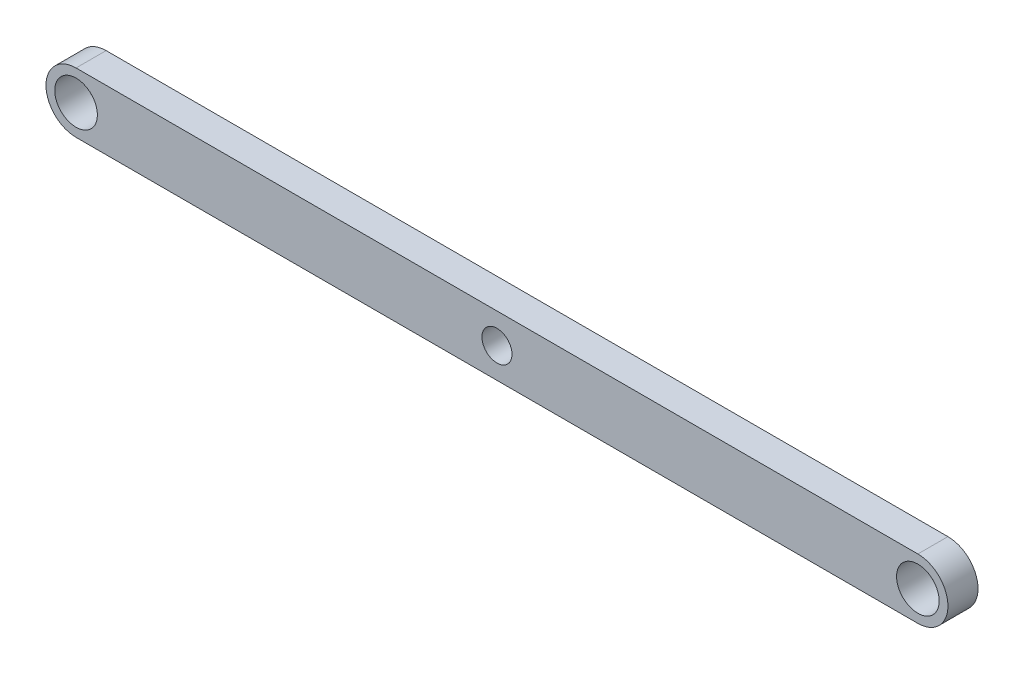
SolidWorks part; units mm, degrees
ref_plane "Front Plane" through (0, 0, 0) normal (0, 0, 1) x (1, 0, 0)
ref_plane "Top Plane" through (0, 0, 0) normal (0, 1, 0) x (1, 0, 0)
ref_plane "Right Plane" through (0, 0, 0) normal (1, 0, 0) x (0, 0, -1)
sketch "Sketch1" plane through (0, 0, 0) normal (0, 0, 1) x (1, 0, 0)
  line L0 (-88.9, 0) -> (88.9, 0) construction
  line L1 (-88.9, 6.35) -> (88.9, 6.35)
  line L2 (-88.9, -6.35) -> (88.9, -6.35)
  arc A0 (-88.9, 6.35) -> (-88.9, -6.35) centre (-88.9, 0) ccw
  arc A1 (88.9, -6.35) -> (88.9, 6.35) centre (88.9, 0) ccw
  circle A2 centre (-88.9, 0) radius 4.5
  circle A3 centre (88.9, 0) radius 4.5
  circle A4 centre (0, 0) radius 3.175
  point P2 (0, 0)
  dimension "D3" = 9
  dimension "D4" = 6.35
  dimension "D1" = 177.8
  dimension "D2" = 12.7
extrude "Boss-Extrude1" add sketch "Sketch1" along normal blind 6.35
